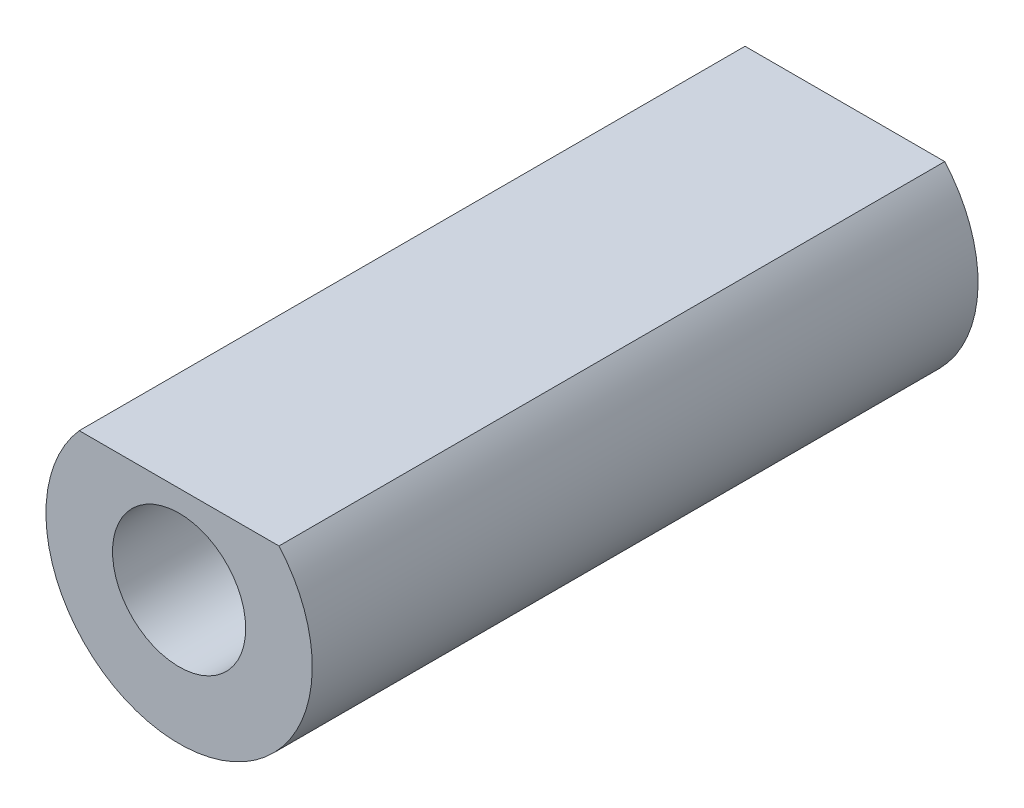
SolidWorks part; units mm, degrees
ref_plane "Front" through (0, 0, 0) normal (0, 0, 1) x (1, 0, 0)
ref_plane "Top" through (0, 0, 0) normal (0, 1, 0) x (1, 0, 0)
ref_plane "Right" through (0, 0, 0) normal (1, 0, 0) x (0, 0, -1)
sketch "Esboço1" plane through (0, 0, 0) normal (0, 1, 0) x (1, 0, 0)
  line L0 (-1, 0) -> (-1, 10)
  line L1 (-1, 10) -> (-2, 10)
  line L2 (-2, 10) -> (-2, 0)
  line L3 (-2, 0) -> (-1, 0)
  line L4 (0, 0) -> (0, 32.4136) construction
  dimension "D1" = 2
  dimension "D2" = 4
  dimension "D3" = 10
revolve "Revolução1" add sketch "Esboço1" angle 360 about L4
sketch "Esboço2" plane through (0, 0, 0) normal (0, 0, 1) x (1, 0, 0)
  line L0 (-1.5, 1.3229) -> (1.5, 1.3229)
  circle A0 centre (0, 0) radius 2 construction
  arc A1 (-1.5, 1.3229) -> (1.5, 1.3229) centre (0, 0) cw
  dimension "D2" = 2
  dimension "D1" = 3
extrude "Corte-extrusão1" cut sketch "Esboço2" against normal through all
